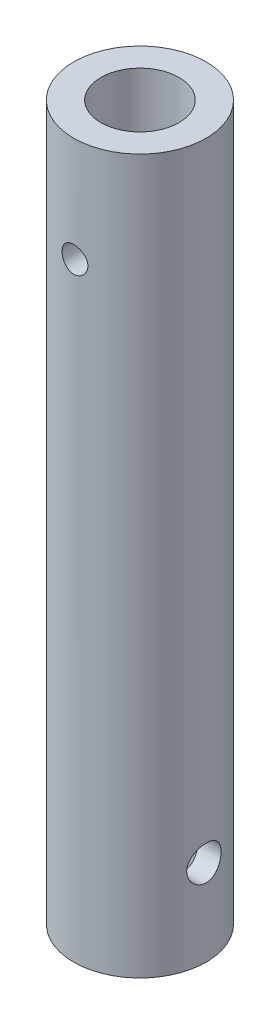
SolidWorks part; units mm, degrees
material "ABS Plastic"
ref_plane "Front Plane" through (0, 0, 0) normal (0, 0, 1) x (1, 0, 0)
ref_plane "Top Plane" through (0, 0, 0) normal (0, 1, 0) x (1, 0, 0)
ref_plane "Right Plane" through (0, 0, 0) normal (1, 0, 0) x (0, 0, -1)
sketch "Sketch1" plane through (0, 0, 0) normal (0, 1, 0) x (1, 0, 0)
  circle A0 centre (0, 0) radius 9.779
  circle A1 centre (0, 0) radius 5.7785
  dimension "D1" = 19.558
  dimension "D2" = 11.557
extrude "Boss-Extrude1" add sketch "Sketch1" along normal blind 105.41
sketch "Sketch2" plane through (0, 0, 0) normal (0, 0, 1) x (1, 0, 0)
  line L0 (9.779, 105.41) -> (-9.779, 105.41) construction
  circle A0 centre (0, 89.916) radius 1.905
  dimension "D1" = 15.494
  dimension "D2" = 3.81
extrude "Cut-Extrude1" cut sketch "Sketch2" against normal through all both and the other way through all
sketch "Sketch3" plane through (0, 0, 0) normal (1, 0, 0) x (0, 0, -1)
  line L0 (-9.779, 0) -> (9.779, 0) construction
  circle A0 centre (0, 12.7) radius 2.54
  dimension "D1" = 12.7
  dimension "D2" = 5.08
extrude "Cut-Extrude2" cut sketch "Sketch3" against normal through all both and the other way through all
sketch "Sketch4" plane through (0, 0, 0) normal (0, -1, 0) x (1, 0, 0)
  circle A0 centre (0, 0) radius 6.604
  dimension "D1" = 13.208
extrude "Cut-Extrude3" cut sketch "Sketch4" against normal blind 77.216
